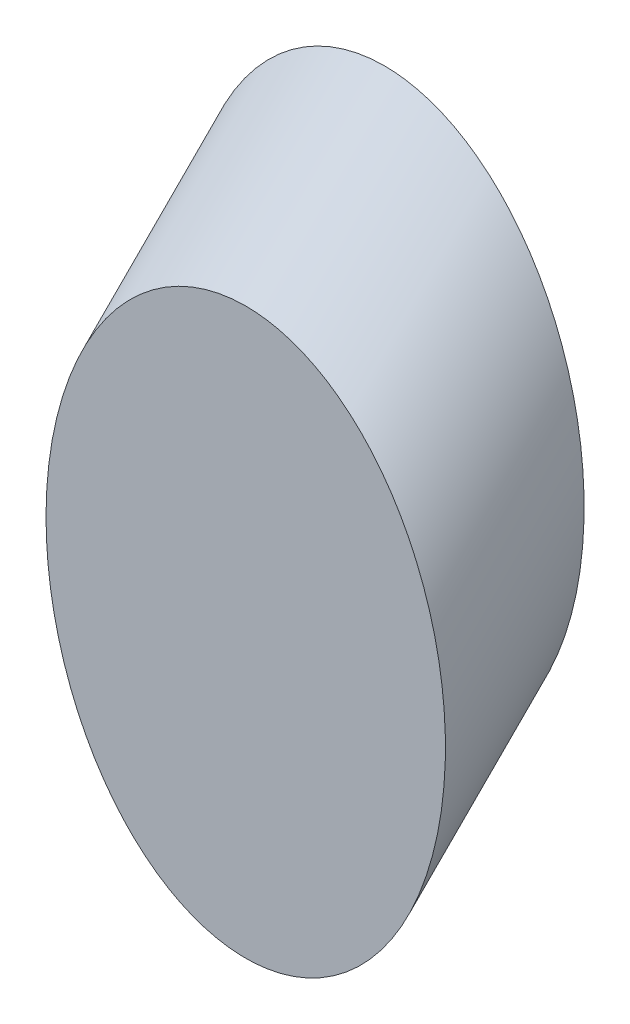
SolidWorks part; units mm, degrees
ref_plane "前视基准面" through (0, 0, 0) normal (0, 0, 1) x (1, 0, 0)
ref_plane "上视基准面" through (0, 0, 0) normal (0, 1, 0) x (1, 0, 0)
ref_plane "右视基准面" through (0, 0, 0) normal (1, 0, 0) x (0, 0, -1)
sketch "草图1" plane through (0, 0, 0) normal (0, 0, 1) x (1, 0, 0)
  ellipse E0 centre (54.3924, 35.7889) end of major axis (54.3924, 10.3289) minor radius 18
  dimension "D1" = 36
  dimension "D2" = 50.92
sketch3d "3D草图2"
  line L0 (55.1123, 61.2285, 0) -> (55.1123, 61.2285, -2.7888)
  line L3 (55.1123, 61.2285, 0) -> (55.1123, 39.6834, 21.5451)
  line L4 (55.1123, 61.2285, 0) -> (55.1123, 28.9476, 0)
  spline S2 degree 3 poles (54.3924, 61.2489, 0) (18.3924, 61.2489, 0) (18.3924, 10.3289, 0) (54.3924, 10.3289, 0) (90.3924, 10.3289, 0) (90.3924, 61.2489, 0) (54.3924, 61.2489, 0) (18.3924, 61.2489, 0) (18.3924, 10.3289, 0) knots -0.5 0 0 0 0.5 0.5 0.5 1 1 1 1.5 1.5 1.5 weights 1 0.333333 0.333333 1 0.333333 0.333333 1 0.333333 0.333333 only from (54.3924, 61.2489, 0) to (54.3924, 61.2489, 0) construction
  dimension "D1" = 45
extrude "凸台-拉伸2" add sketch "草图1" along direction (0, -0.7071, 0.7071) on the side against the normal blind 17.678
